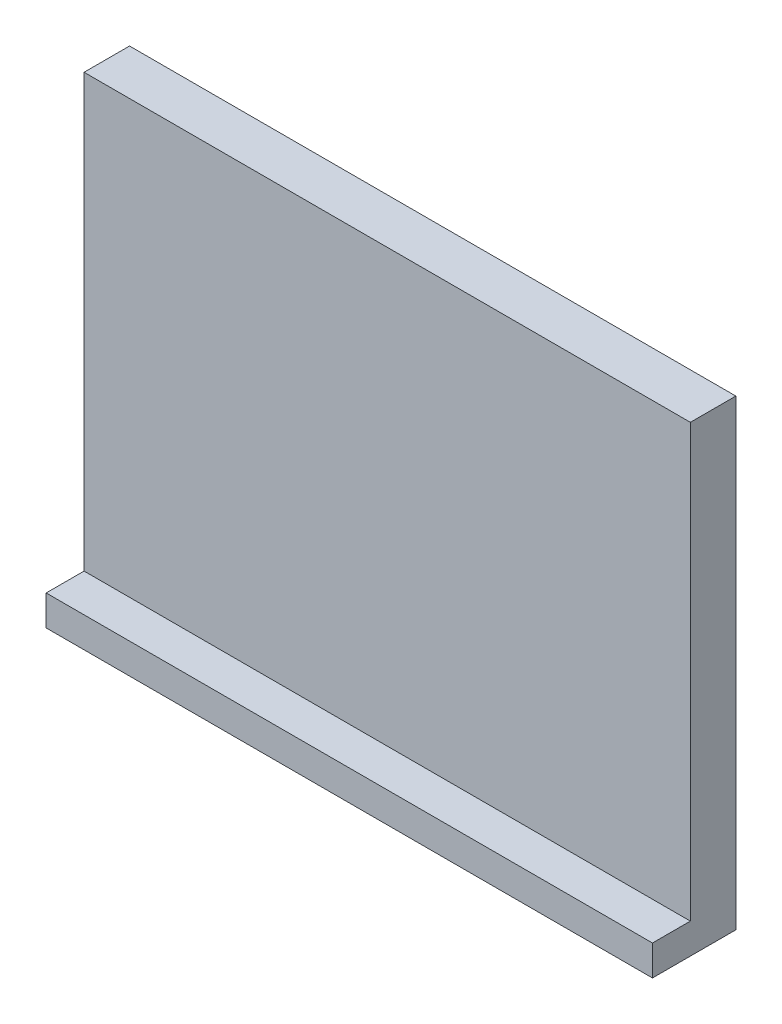
SolidWorks part; units mm, degrees
ref_plane "Alzado" through (0, 0, 0) normal (0, 0, 1) x (1, 0, 0)
ref_plane "Planta" through (0, 0, 0) normal (0, 1, 0) x (1, 0, 0)
ref_plane "Vista lateral" through (0, 0, 0) normal (1, 0, 0) x (0, 0, -1)
sketch "Croquis1" plane through (0, 0, 0) normal (0, 0, 1) x (1, 0, 0)
  line L1 (0, 0) -> (80, 0)
  line L2 (0, 0) -> (0, 61)
  line L3 (0, 61) -> (80, 61)
  line L4 (80, 0) -> (80, 61)
  dimension "D1" = 80
  dimension "D2" = 61
extrude "Saliente-Extruir1" add sketch "Croquis1" along normal blind 6
sketch "Croquis2" plane through (0, 0, 6) normal (0, 0, 1) x (1, 0, 0)
  line L0 (80, 0) -> (80, 61) construction
  line L1 (0, 0) -> (80, 0)
  line L2 (0, 0) -> (0, 4)
  line L3 (0, 4) -> (80, 4)
  line L4 (80, 0) -> (80, 4)
  dimension "D1" = 4
extrude "Saliente-Extruir2" add sketch "Croquis2" along normal blind 5
